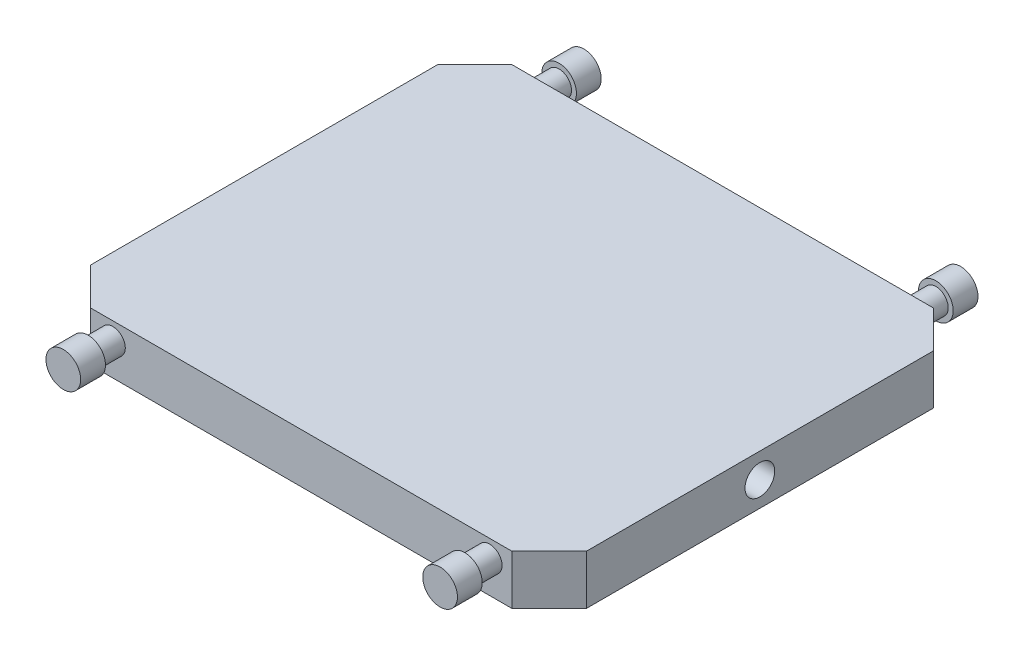
SolidWorks part; units mm, degrees
ref_plane "Front Plane" through (0, 0, 0) normal (0, 0, 1) x (1, 0, 0)
ref_plane "Top Plane" through (0, 0, 0) normal (0, 1, 0) x (1, 0, 0)
ref_plane "Right Plane" through (0, 0, 0) normal (1, 0, 0) x (0, 0, -1)
sketch "Sketch1" plane through (0, 0, 0) normal (0, 1, 0) x (1, 0, 0)
  line L0 (0, 310) -> (30, 340)
  line L1 (30, 0) -> (370, 0)
  line L2 (0, 30) -> (0, 310)
  line L3 (30, 340) -> (370, 340)
  line L4 (400, 30) -> (400, 310)
  line L5 (0, 30) -> (30, 0)
  line L6 (370, 0) -> (400, 30)
  line L7 (370, 340) -> (400, 310)
  point P0 (0, 0)
  point P1 (400, 340)
  point P2 (0, 340)
  point P3 (400, 0)
  dimension "D1" = 340
  dimension "D2" = 400
extrude "Boss-Extrude1" add sketch "Sketch1" along normal blind 40
sketch "Sketch2" plane through (0, 0, 0) normal (-1, 0, 0) x (0, 0, 1)
  line L0 (-310, 40) -> (-30, 40) construction
  circle A0 centre (-170, 20) radius 12
  point P5 (-170, 40)
  dimension "D1" = 24
extrude "Cut-Extrude1" cut sketch "Sketch2" against normal through all
sketch "Sketch3" plane through (0, 0, 0) normal (0, 0, 1) x (1, 0, 0)
  line L0 (30, 40) -> (370, 40) construction
  line L1 (30, 40) -> (30, 0) construction
  line L2 (200, 55.1918) -> (200, -40.6233) construction
  circle A0 centre (48, 26) radius 10
  circle A1 centre (352, 26) radius 10
  dimension "D1" = 20
  dimension "D2" = 14
  dimension "D3" = 18
extrude "Boss-Extrude2" add sketch "Sketch3" along normal blind 20
sketch "Sketch4" plane through (0, 0, 20) normal (0, 0, 1) x (1, 0, 0)
  circle A0 centre (48, 26) radius 14
  circle A1 centre (352, 26) radius 14
extrude "Boss-Extrude3" add sketch "Sketch4" along normal blind 20
ref_plane "Plane1" through (0, 0, -170) normal (0, 0, 1) x (1, 0, 0)
mirror "Mirror1" about plane through (0, 0, -170) normal (0, 0, 1) of "Boss-Extrude3", "Boss-Extrude2"
